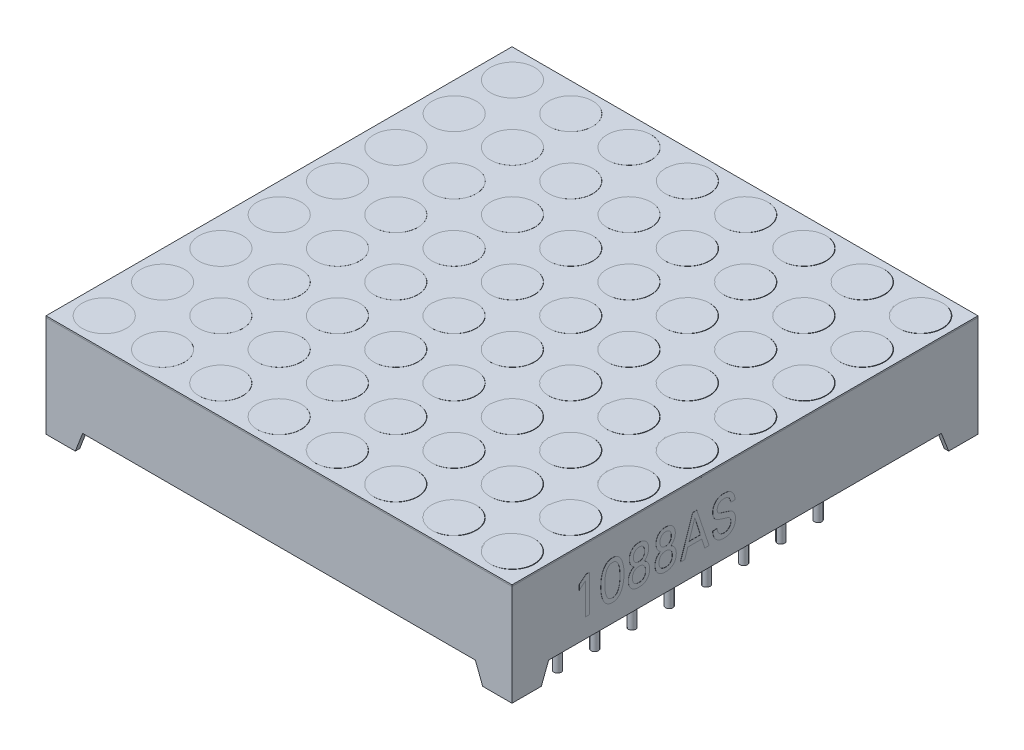
SolidWorks part; units mm, degrees
ref_plane "Front Plane" through (0, 0, 0) normal (0, 0, 1) x (1, 0, 0)
ref_plane "Top Plane" through (0, 0, 0) normal (0, 1, 0) x (1, 0, 0)
ref_plane "Right Plane" through (0, 0, 0) normal (1, 0, 0) x (0, 0, -1)
sketch "Sketch1" plane through (0, 0, 0) normal (0, 1, 0) x (1, 0, 0)
  line L0 (3.975, 31.8) -> (3.975, 0) construction
  line L1 (0, 0) -> (31.8, 0)
  line L2 (0, 0) -> (0, 31.8)
  line L3 (0, 31.8) -> (31.8, 31.8)
  line L4 (31.8, 0) -> (31.8, 31.8)
  line L5 (7.955, 31.8) -> (7.955, 0) construction
  line L6 (11.935, 31.8) -> (11.935, 0) construction
  line L7 (15.915, 31.8) -> (15.915, 0) construction
  line L8 (19.895, 31.8) -> (19.895, 0) construction
  line L9 (23.875, 31.8) -> (23.875, 0) construction
  line L10 (27.855, 31.8) -> (27.855, 0) construction
  line L11 (0, 3.975) -> (31.8, 3.975) construction
  line L12 (0, 7.955) -> (31.8, 7.955) construction
  line L13 (0, 11.935) -> (31.8, 11.935) construction
  line L14 (0, 15.915) -> (31.8, 15.915) construction
  line L15 (0, 19.895) -> (31.8, 19.895) construction
  line L16 (0, 23.875) -> (31.8, 23.875) construction
  line L17 (0, 27.855) -> (31.8, 27.855) construction
  line L18 (0, 0) -> (3.975, 3.975) construction
  line L19 (0, 3.975) -> (3.975, 0) construction
  circle A0 centre (1.9875, 1.9875) radius 1.5
  circle A1 centre (5.9675, 1.9875) radius 1.5
  circle A2 centre (9.9475, 1.9875) radius 1.5
  circle A3 centre (13.9275, 1.9875) radius 1.5
  circle A4 centre (17.9075, 1.9875) radius 1.5
  circle A5 centre (21.8875, 1.9875) radius 1.5
  circle A6 centre (25.8675, 1.9875) radius 1.5
  circle A7 centre (29.8475, 1.9875) radius 1.5
  circle A8 centre (5.9675, 5.9675) radius 1.5
  circle A9 centre (9.9475, 5.9675) radius 1.5
  circle A10 centre (13.9275, 5.9675) radius 1.5
  circle A11 centre (17.9075, 5.9675) radius 1.5
  circle A12 centre (21.8875, 5.9675) radius 1.5
  circle A13 centre (25.8675, 5.9675) radius 1.5
  circle A14 centre (29.8475, 5.9675) radius 1.5
  circle A15 centre (5.9675, 9.9475) radius 1.5
  circle A16 centre (9.9475, 9.9475) radius 1.5
  circle A17 centre (13.9275, 9.9475) radius 1.5
  circle A18 centre (17.9075, 9.9475) radius 1.5
  circle A19 centre (21.8875, 9.9475) radius 1.5
  circle A20 centre (25.8675, 9.9475) radius 1.5
  circle A21 centre (29.8475, 9.9475) radius 1.5
  circle A22 centre (5.9675, 13.9275) radius 1.5
  circle A23 centre (9.9475, 13.9275) radius 1.5
  circle A24 centre (13.9275, 13.9275) radius 1.5
  circle A25 centre (17.9075, 13.9275) radius 1.5
  circle A26 centre (21.8875, 13.9275) radius 1.5
  circle A27 centre (25.8675, 13.9275) radius 1.5
  circle A28 centre (29.8475, 13.9275) radius 1.5
  circle A29 centre (5.9675, 17.9075) radius 1.5
  circle A30 centre (9.9475, 17.9075) radius 1.5
  circle A31 centre (13.9275, 17.9075) radius 1.5
  circle A32 centre (17.9075, 17.9075) radius 1.5
  circle A33 centre (21.8875, 17.9075) radius 1.5
  circle A34 centre (25.8675, 17.9075) radius 1.5
  circle A35 centre (29.8475, 17.9075) radius 1.5
  circle A36 centre (5.9675, 21.8875) radius 1.5
  circle A37 centre (9.9475, 21.8875) radius 1.5
  circle A38 centre (13.9275, 21.8875) radius 1.5
  circle A39 centre (17.9075, 21.8875) radius 1.5
  circle A40 centre (21.8875, 21.8875) radius 1.5
  circle A41 centre (25.8675, 21.8875) radius 1.5
  circle A42 centre (29.8475, 21.8875) radius 1.5
  circle A43 centre (5.9675, 25.8675) radius 1.5
  circle A44 centre (9.9475, 25.8675) radius 1.5
  circle A45 centre (13.9275, 25.8675) radius 1.5
  circle A46 centre (17.9075, 25.8675) radius 1.5
  circle A47 centre (21.8875, 25.8675) radius 1.5
  circle A48 centre (25.8675, 25.8675) radius 1.5
  circle A49 centre (29.8475, 25.8675) radius 1.5
  circle A50 centre (5.9675, 29.8475) radius 1.5
  circle A51 centre (9.9475, 29.8475) radius 1.5
  circle A52 centre (13.9275, 29.8475) radius 1.5
  circle A53 centre (17.9075, 29.8475) radius 1.5
  circle A54 centre (21.8875, 29.8475) radius 1.5
  circle A55 centre (25.8675, 29.8475) radius 1.5
  circle A56 centre (29.8475, 29.8475) radius 1.5
  circle A57 centre (1.9875, 5.9675) radius 1.5
  circle A58 centre (1.9875, 9.9475) radius 1.5
  circle A59 centre (1.9875, 13.9275) radius 1.5
  circle A60 centre (1.9875, 17.9075) radius 1.5
  circle A61 centre (1.9875, 21.8875) radius 1.5
  circle A62 centre (1.9875, 25.8675) radius 1.5
  circle A63 centre (1.9875, 29.8475) radius 1.5
  dimension "D7" = 8
  dimension "D1" = 31.8
  dimension "D2" = 31.8
  dimension "D3" = 3.975
  dimension "D5" = 3.975
  dimension "D4" = 7
  dimension "D6" = 7
  dimension "D8" = 8
extrude "TOP MASK" add sketch "Sketch1" against normal blind 0.1
sketch "Sketch2" plane through (0, -0.1, 0) normal (0, -1, 0) x (1, 0, 0)
  line L0 (31.8, 0) -> (31.8, -31.8) construction
  line L1 (31.8, -31.8) -> (0, -31.8) construction
  line L2 (0, -31.8) -> (0, 0) construction
  line L3 (0, 0) -> (31.8, 0) construction
  line L4 (31.8, 0) -> (31.8, -31.8)
  line L5 (31.8, -31.8) -> (0, -31.8)
  line L6 (0, -31.8) -> (0, 0)
  line L7 (0, 0) -> (31.8, 0)
  line L8 (31.5, -0.3) -> (31.5, -31.5)
  line L9 (31.5, -31.5) -> (0.3, -31.5)
  line L10 (0.3, -31.5) -> (0.3, -0.3)
  line L11 (0.3, -0.3) -> (31.5, -0.3)
  dimension "D1" = 0.3
extrude "SIDES" add sketch "Sketch2" along normal blind 6.9 separate body
sketch "Sketch3" plane through (0, 0, -31.8) normal (0, 0, -1) x (-1, 0, 0)
  line L0 (-2, -7) -> (-29.8, -7)
  line L2 (-2, -7) -> (-2.5, -5.7)
  line L3 (-29.8, -7) -> (-29.8035, -7.0031)
  line L8 (-29.8, -7) -> (-29.3, -5.7)
  line L9 (-29.3, -5.7) -> (-2.5, -5.7)
  line M7 (-31.8, -7) -> (0, -7)
extrude "Cut-Extrude2" cut sketch "Sketch3" against normal through all both and the other way through all contours L9 L8 L2 M7
sketch "Sketch4" plane through (0, 0, 0) normal (-1, 0, 0) x (0, 0, 1)
  line L0 (-29.8, -7) -> (-29.3, -5.7)
  line L1 (0, -7) -> (-31.8, -7) construction
  line L2 (-29.3, -5.7) -> (-2.5, -5.7)
  line L3 (-2.5, -5.7) -> (-2, -7)
  line L4 (-2, -7) -> (-29.8, -7)
  line L5 (-31.8, -7) -> (-31.8, -0.1) construction
  line L6 (0, -7) -> (0, -0.1) construction
  line L7 (0, -5.7) -> (-0.3, -5.7) construction
  dimension "D1" = 2
  dimension "D2" = 2.5
  dimension "D3" = 2
  dimension "D4" = 2.5
extrude "Cut-Extrude3" cut sketch "Sketch4" against normal through all
sketch "Sketch5" plane through (0, 0, 0) normal (0, 1, 0) x (1, 0, 0)
  circle A0 centre (1.9875, 1.9875) radius 1.5 construction
  circle A1 centre (1.9875, 1.9875) radius 1.5
  circle A2 centre (5.9625, 1.9875) radius 1.5
  circle A3 centre (9.9375, 1.9875) radius 1.5
  circle A4 centre (13.9125, 1.9875) radius 1.5
  circle A5 centre (17.8875, 1.9875) radius 1.5
  circle A6 centre (21.8625, 1.9875) radius 1.5
  circle A7 centre (25.8375, 1.9875) radius 1.5
  circle A8 centre (29.8125, 1.9875) radius 1.5
  circle A9 centre (5.9625, 5.9675) radius 1.5
  circle A10 centre (9.9375, 5.9675) radius 1.5
  circle A11 centre (13.9125, 5.9675) radius 1.5
  circle A12 centre (17.8875, 5.9675) radius 1.5
  circle A13 centre (21.8625, 5.9675) radius 1.5
  circle A14 centre (25.8375, 5.9675) radius 1.5
  circle A15 centre (29.8125, 5.9675) radius 1.5
  circle A16 centre (5.9625, 9.9475) radius 1.5
  circle A17 centre (9.9375, 9.9475) radius 1.5
  circle A18 centre (13.9125, 9.9475) radius 1.5
  circle A19 centre (17.8875, 9.9475) radius 1.5
  circle A20 centre (21.8625, 9.9475) radius 1.5
  circle A21 centre (25.8375, 9.9475) radius 1.5
  circle A22 centre (29.8125, 9.9475) radius 1.5
  circle A23 centre (5.9625, 13.9275) radius 1.5
  circle A24 centre (9.9375, 13.9275) radius 1.5
  circle A25 centre (13.9125, 13.9275) radius 1.5
  circle A26 centre (17.8875, 13.9275) radius 1.5
  circle A27 centre (21.8625, 13.9275) radius 1.5
  circle A28 centre (25.8375, 13.9275) radius 1.5
  circle A29 centre (29.8125, 13.9275) radius 1.5
  circle A30 centre (5.9625, 17.9075) radius 1.5
  circle A31 centre (9.9375, 17.9075) radius 1.5
  circle A32 centre (13.9125, 17.9075) radius 1.5
  circle A33 centre (17.8875, 17.9075) radius 1.5
  circle A34 centre (21.8625, 17.9075) radius 1.5
  circle A35 centre (25.8375, 17.9075) radius 1.5
  circle A36 centre (29.8125, 17.9075) radius 1.5
  circle A37 centre (5.9625, 21.8875) radius 1.5
  circle A38 centre (9.9375, 21.8875) radius 1.5
  circle A39 centre (13.9125, 21.8875) radius 1.5
  circle A40 centre (17.8875, 21.8875) radius 1.5
  circle A41 centre (21.8625, 21.8875) radius 1.5
  circle A42 centre (25.8375, 21.8875) radius 1.5
  circle A43 centre (29.8125, 21.8875) radius 1.5
  circle A44 centre (5.9625, 25.8675) radius 1.5
  circle A45 centre (9.9375, 25.8675) radius 1.5
  circle A46 centre (13.9125, 25.8675) radius 1.5
  circle A47 centre (17.8875, 25.8675) radius 1.5
  circle A48 centre (21.8625, 25.8675) radius 1.5
  circle A49 centre (25.8375, 25.8675) radius 1.5
  circle A50 centre (29.8125, 25.8675) radius 1.5
  circle A51 centre (5.9625, 29.8475) radius 1.5
  circle A52 centre (9.9375, 29.8475) radius 1.5
  circle A53 centre (13.9125, 29.8475) radius 1.5
  circle A54 centre (17.8875, 29.8475) radius 1.5
  circle A55 centre (21.8625, 29.8475) radius 1.5
  circle A56 centre (25.8375, 29.8475) radius 1.5
  circle A57 centre (29.8125, 29.8475) radius 1.5
  circle A58 centre (1.9875, 5.9675) radius 1.5
  circle A59 centre (1.9875, 9.9475) radius 1.5
  circle A60 centre (1.9875, 13.9275) radius 1.5
  circle A61 centre (1.9875, 17.9075) radius 1.5
  circle A62 centre (1.9875, 21.8875) radius 1.5
  circle A63 centre (1.9875, 25.8675) radius 1.5
  circle A64 centre (1.9875, 29.8475) radius 1.5
  dimension "D1" = 8
  dimension "D2" = 8
extrude "Boss-Extrude3" add sketch "Sketch5" against normal blind 0.1 separate body
sketch "Sketch6" plane through (0, -5.7, 0) normal (0, -1, 0) x (1, 0, 0)
  line L1 (0.3, -0.3) -> (31.5, -0.3)
  line L2 (0.3, -0.3) -> (0.3, -31.5)
  line L3 (0.3, -31.5) -> (31.5, -31.5)
  line L4 (31.5, -0.3) -> (31.5, -31.5)
extrude "Boss-Extrude4" add sketch "Sketch6" against normal up to surface (4.1 mm away) from offset 1.5 separate body up to face at (1.9875, -0.1, -28.3475) offset against normal yes
sketch "Sketch7" plane through (0, -4.2, 0) normal (0, -1, 0) x (1, 0, 0)
  line L0 (15.9, 0) -> (15.9, -31.8) construction
  line L1 (29.3, 0) -> (2.5, 0) construction
  line L2 (2.5, -31.8) -> (29.3, -31.8) construction
  line L3 (0, -15.9) -> (31.8, -15.9) construction
  line L4 (0, -2.5) -> (0, -29.3) construction
  line L5 (31.8, -2.5) -> (31.8, -29.3) construction
  circle A0 centre (3.9, -14.63) radius 0.25
  circle A1 centre (3.9, -12.09) radius 0.25
  circle A2 centre (3.9, -9.55) radius 0.25
  circle A3 centre (3.9, -7.01) radius 0.25
  circle A4 centre (27.9, -7.01) radius 0.25
  circle A5 centre (27.9, -9.55) radius 0.25
  circle A6 centre (27.9, -12.09) radius 0.25
  circle A7 centre (27.9, -14.63) radius 0.25
  circle A8 centre (27.9, -17.17) radius 0.25
  circle A9 centre (27.9, -19.71) radius 0.25
  circle A10 centre (27.9, -22.25) radius 0.25
  circle A11 centre (27.9, -24.79) radius 0.25
  circle A12 centre (3.9, -24.79) radius 0.25
  circle A13 centre (3.9, -22.25) radius 0.25
  circle A14 centre (3.9, -19.71) radius 0.25
  circle A15 centre (3.9, -17.17) radius 0.25
  dimension "D1" = 0.5
  dimension "D2" = 1.27
  dimension "D3" = 12
  dimension "D4" = 4
extrude "Boss-Extrude5" add sketch "Sketch7" along normal blind 6.3 from surface at 0 separate body starting at face at (15.9, -4.2, -15.9)
sketch "Sketch8" plane through (31.8, 0, 0) normal (1, 0, 0) x (0, 0, -1)
  text T0 "1088AS" font "Utah" height 2.5
extrude "1088AS" add sketch "Sketch8" along normal blind 0.01 separate body
